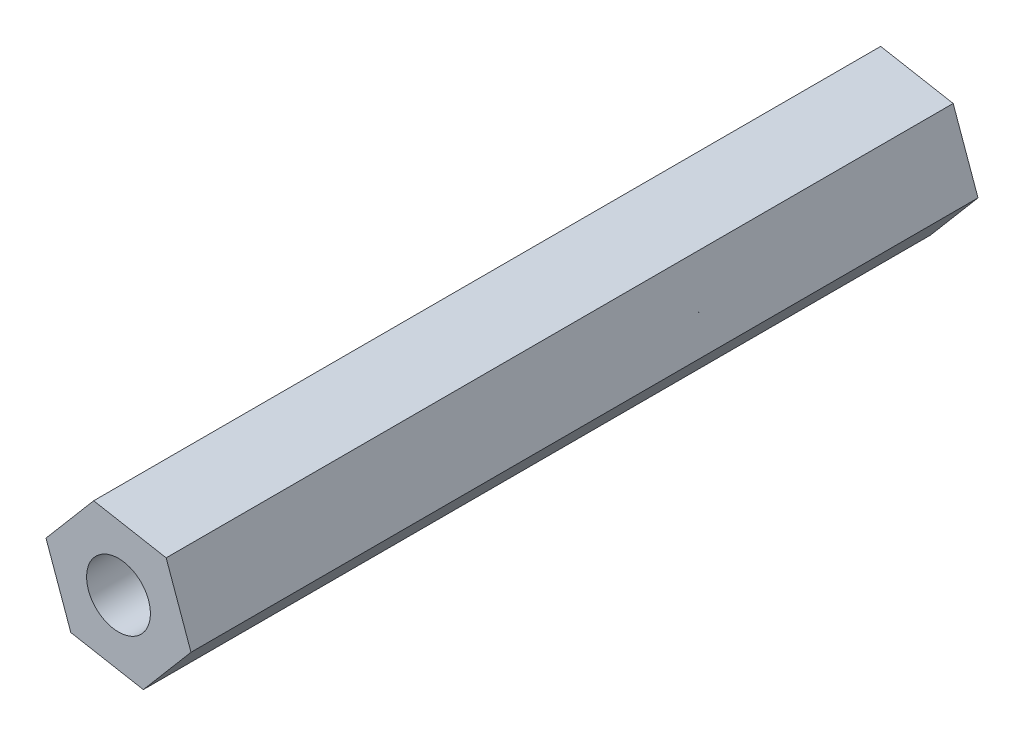
SolidWorks part; units mm, degrees
ref_plane "Plano frontal" through (0, 0, 0) normal (0, 0, 1) x (1, 0, 0)
ref_plane "Plano superior" through (0, 0, 0) normal (0, 1, 0) x (1, 0, 0)
ref_plane "Plano direito" through (0, 0, 0) normal (1, 0, 0) x (0, 0, -1)
sketch "Esboço1" plane through (0, 0, 0) normal (0, 0, 1) x (1, 0, 0)
  line L1 (12.9332, -4.1439) -> (9.5251, -3.5237)
  line L2 (9.5251, -3.5237) -> (7.2839, -6.1651)
  line L3 (7.2839, -6.1651) -> (8.4508, -9.4267)
  line L4 (8.4508, -9.4267) -> (11.8589, -10.0469)
  line L5 (11.8589, -10.0469) -> (14.1001, -7.4055)
  line L6 (14.1001, -7.4055) -> (12.9332, -4.1439)
  circle A0 centre (10.692, -6.7853) radius 3 construction
extrude "Ressalto-extrusão1" add sketch "Esboço1" along normal blind 37
sketch "Esboço4" plane through (0, 0, 0) normal (0, 0, -1) x (-1, 0, 0)
  line L1 (-12.9332, -4.1439) -> (-9.5251, -3.5237) construction
  circle A0 centre (-10.692, -6.7853) radius 1.5
  dimension "D1" = 3
extrude "Corte-extrusão2" cut sketch "Esboço4" against normal blind 40
